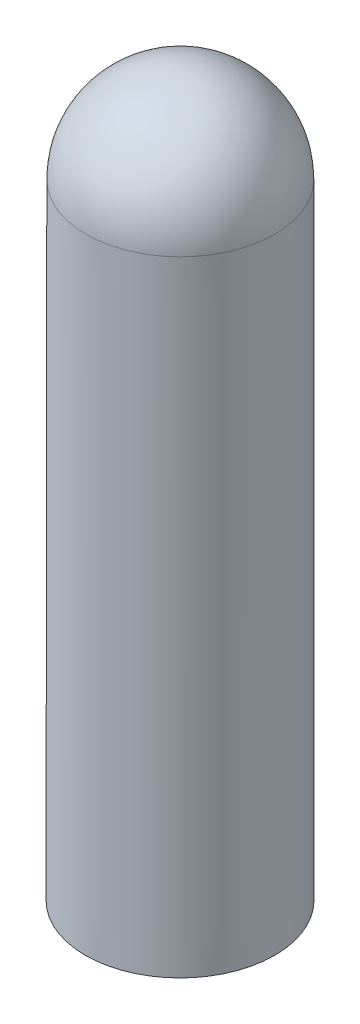
SolidWorks part; units mm, degrees
ref_plane "Front Plane" through (0, 0, 0) normal (0, 0, 1) x (1, 0, 0)
ref_plane "Top Plane" through (0, 0, 0) normal (0, 1, 0) x (1, 0, 0)
ref_plane "Right Plane" through (0, 0, 0) normal (1, 0, 0) x (0, 0, -1)
sketch "Sketch1" plane through (0, 0, 0) normal (0, 0, 1) x (1, 0, 0)
  line L0 (1.9962, -2.0038) -> (1.9962, -15.2142)
  line L1 (1.9962, -15.2142) -> (-0.0076, -15.2142)
  line L2 (-0.0076, -15.2142) -> (0, 0)
  arc A0 (0, 0) -> (1.9962, -2.0038) centre (-0.0038, -2) cw
  dimension "D1" = 2
revolve "Revolve1" add sketch "Sketch1" angle 360 about L2
